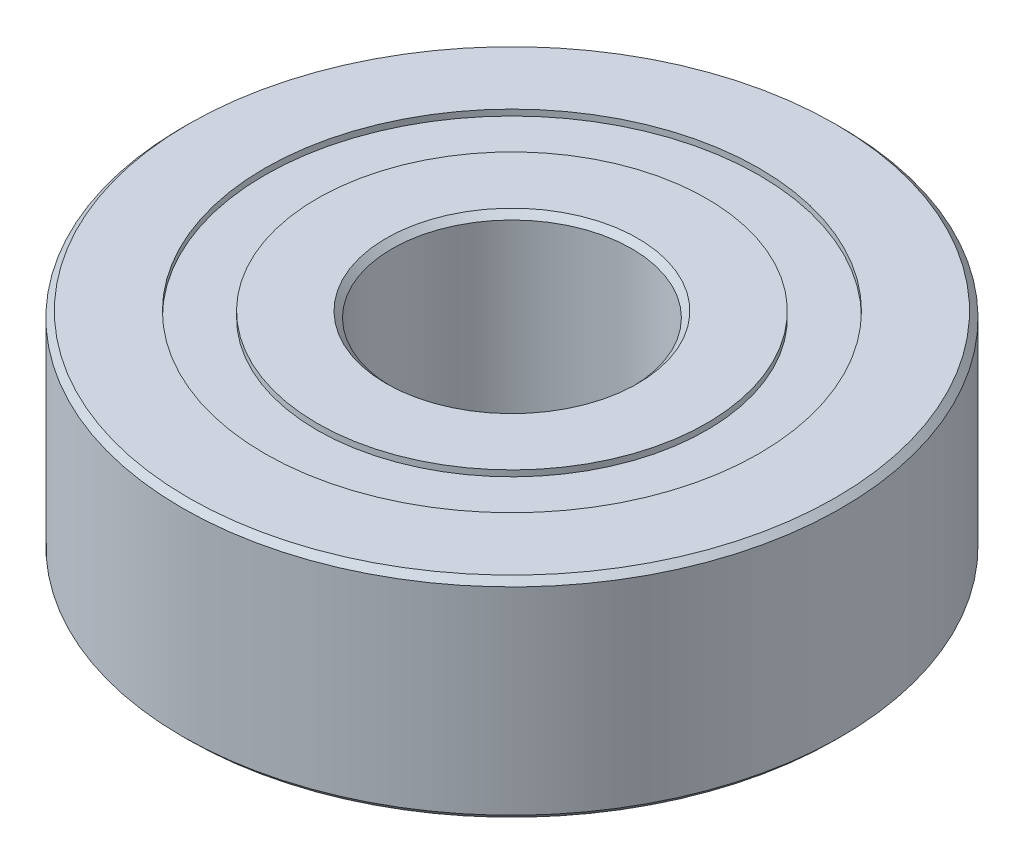
SolidWorks part; units mm, degrees
ref_plane "Front Plane" through (0, 0, 0) normal (0, 0, 1) x (1, 0, 0)
ref_plane "Top Plane" through (0, 0, 0) normal (0, 1, 0) x (1, 0, 0)
ref_plane "Right Plane" through (0, 0, 0) normal (1, 0, 0) x (0, 0, -1)
sketch "Sketch1" plane through (0, 0, 0) normal (0, 1, 0) x (1, 0, 0)
  circle A0 centre (0, 0) radius 11
  circle A1 centre (0, 0) radius 4
  dimension "D1" = 22
  dimension "D2" = 8
extrude "Boss-Extrude1" add sketch "Sketch1" along normal blind 7
sketch "Sketch2" plane through (0, 7, 0) normal (0, 1, 0) x (1, 0, 0)
  circle A0 centre (0, 0) radius 6.5
  circle A1 centre (0, 0) radius 8.25
  dimension "D1" = 16.5
  dimension "D2" = 13
extrude "Cut-Extrude1" cut sketch "Sketch2" against normal blind 0.2
sketch "Sketch3" plane through (0, 0, 0) normal (0, -1, 0) x (1, 0, 0)
  circle A0 centre (0, 0) radius 6.5 construction
  circle A1 centre (0, 0) radius 8.25
  circle A2 centre (0, 0) radius 8.25
  circle A3 centre (0, 0) radius 6.5
  dimension "D1" = 0
extrude "Cut-Extrude2" cut sketch "Sketch3" against normal blind 0.2
chamfer "Chamfer1" distance 0.2 angle 45
